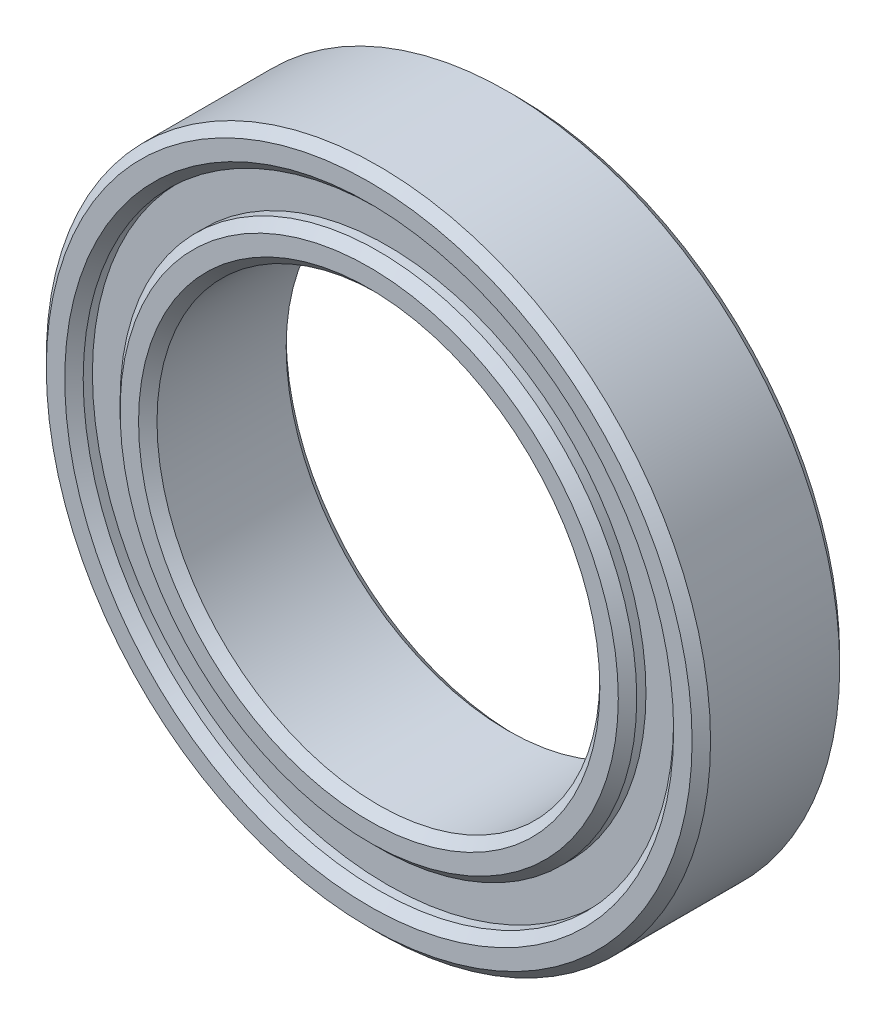
SolidWorks part; units mm, degrees
material "AISI 316 Stainless Steel Sheet (SS)"
ref_plane "Front Plane" through (0, 0, 0) normal (0, 0, 1) x (1, 0, 0)
ref_plane "Top Plane" through (0, 0, 0) normal (0, 1, 0) x (1, 0, 0)
ref_plane "Right Plane" through (0, 0, 0) normal (1, 0, 0) x (0, 0, -1)
sketch "Sketch2" plane through (0, 0, 0) normal (0, 0, 1) x (1, 0, 0)
  circle A0 centre (0, 0) radius 9
  circle A1 centre (0, 0) radius 6
  dimension "D1" = 18
  dimension "D2" = 12
extrude "Boss-Extrude1" add sketch "Sketch2" along normal blind 4
chamfer "Chamfer2" distance 0.25 angle 45 4 edges at (6, 0, 4) (9, 0, 4) (9, 0, 0) (6, 0, 0)
sketch "Sketch3" plane through (0, 0, 0) normal (0, 0, -1) x (-1, 0, 0)
  circle A0 centre (0, 0) radius 7
  circle A1 centre (0, 0) radius 8
  dimension "D1" = 14
  dimension "D2" = 16
ref_plane "Plane1" through (0, 0, 2) normal (0, 0, -1) x (-1, 0, 0)
extrude "Cut-Extrude2" cut sketch "Sketch3" against normal blind 0.5
sketch "Sketch4" plane through (0, 0, 4) normal (0, 0, 1) x (1, 0, 0)
  circle A0 centre (0, 0) radius 7
  circle A1 centre (0, 0) radius 8
  dimension "D1" = 16
  dimension "D2" = 14
extrude "Cut-Extrude3" cut sketch "Sketch4" against normal blind 0.5
chamfer "Chamfer3" distance 0.25 angle 45 4 edges at (7, 0, 4) (8, 0, 4) (-7, 0, 0) (-8, 0, 0)
